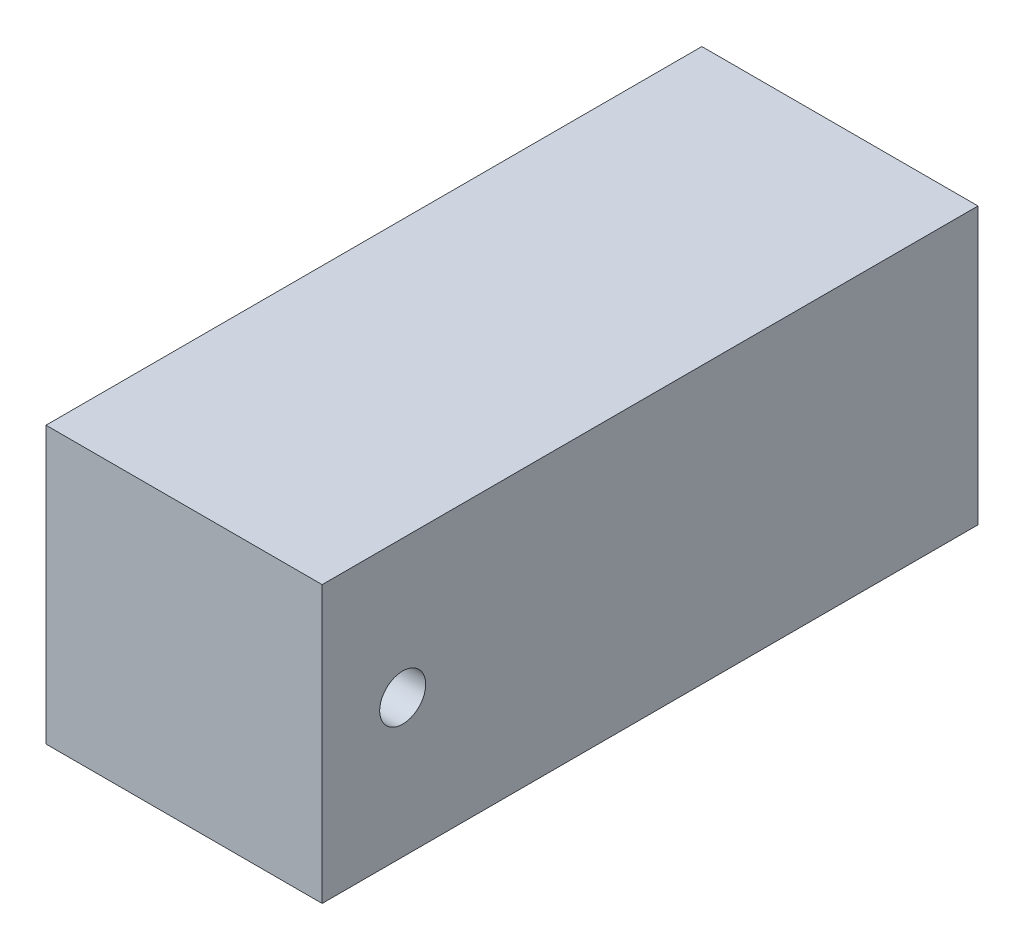
SolidWorks part; units mm, degrees
ref_plane "Front Plane" through (0, 0, 0) normal (0, 0, 1) x (1, 0, 0)
ref_plane "Top Plane" through (0, 0, 0) normal (0, 1, 0) x (1, 0, 0)
ref_plane "Right Plane" through (0, 0, 0) normal (1, 0, 0) x (0, 0, -1)
sketch "Sketch1" plane through (0, 0, 0) normal (0, 1, 0) x (1, 0, 0)
  line L1 (-38.1, -90.4875) -> (38.1, -90.4875)
  line L2 (-38.1, -90.4875) -> (-38.1, 90.4875)
  line L3 (-38.1, 90.4875) -> (38.1, 90.4875)
  line L4 (38.1, -90.4875) -> (38.1, 90.4875)
  line L5 (-38.1, -90.4875) -> (38.1, 90.4875) construction
  line L6 (-38.1, 90.4875) -> (38.1, -90.4875) construction
  point P0 (0, 0)
  dimension "D1" = 180.975
  dimension "D2" = 76.2
extrude "Boss-Extrude1" add sketch "Sketch1" along normal blind 76.2
sketch "Sketch2" plane through (38.1, 0, 0) normal (1, 0, 0) x (0, 0, -1)
  line L0 (-68.2625, 38.1) -> (-90.4875, 38.1) construction
  line L1 (-90.4875, 76.2) -> (-90.4875, 0) construction
  line L2 (90.4875, 76.2) -> (90.4875, 0) construction
  circle A0 centre (-68.2625, 38.1) radius 6.35
  dimension "D1" = 12.7
  dimension "D2" = 158.75
extrude "Cut-Extrude1" cut sketch "Sketch2" against normal blind 76.2
